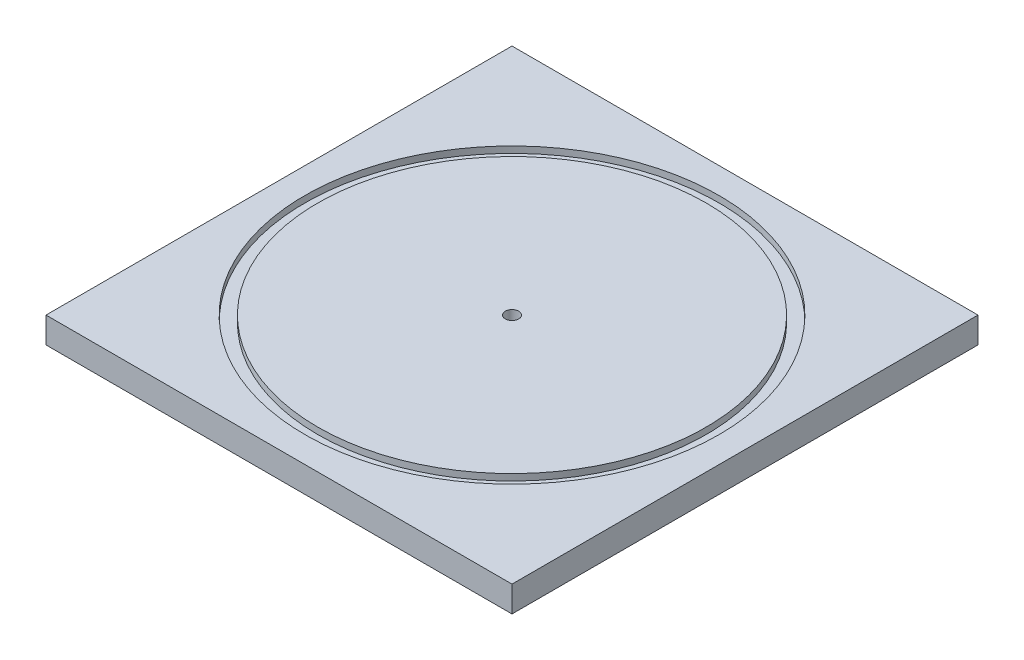
SolidWorks part; units mm, degrees
ref_plane "Front Plane" through (0, 0, 0) normal (0, 0, 1) x (1, 0, 0)
ref_plane "Top Plane" through (0, 0, 0) normal (0, 1, 0) x (1, 0, 0)
ref_plane "Right Plane" through (0, 0, 0) normal (1, 0, 0) x (0, 0, -1)
sketch "Sketch1" plane through (0, 0, 0) normal (0, 1, 0) x (1, 0, 0)
  line L1 (57.15, -57.15) -> (-57.15, -57.15)
  line L2 (57.15, -57.15) -> (57.15, 57.15)
  line L3 (57.15, 57.15) -> (-57.15, 57.15)
  line L4 (-57.15, -57.15) -> (-57.15, 57.15)
  line L5 (57.15, -57.15) -> (-57.15, 57.15) construction
  line L6 (57.15, 57.15) -> (-57.15, -57.15) construction
  point P0 (0, 0)
  dimension "D1" = 114.3
extrude "Boss-Extrude1" add sketch "Sketch1" along normal blind 6.35
sketch "Sketch2" plane through (0, 6.35, 0) normal (0, 1, 0) x (1, 0, 0)
  circle A0 centre (0, 0) radius 47.625
  dimension "D1" = 95.25
extrude "Cut-Extrude-Thin1" cut sketch "Sketch2" against normal blind 1.5875 thin
sketch "Sketch3" plane through (0, 6.35, 0) normal (0, 1, 0) x (1, 0, 0)
  circle A0 centre (0, 0) radius 1.651
  dimension "D1" = 3.302
extrude "Cut-Extrude1" cut sketch "Sketch3" against normal blind 3.175
